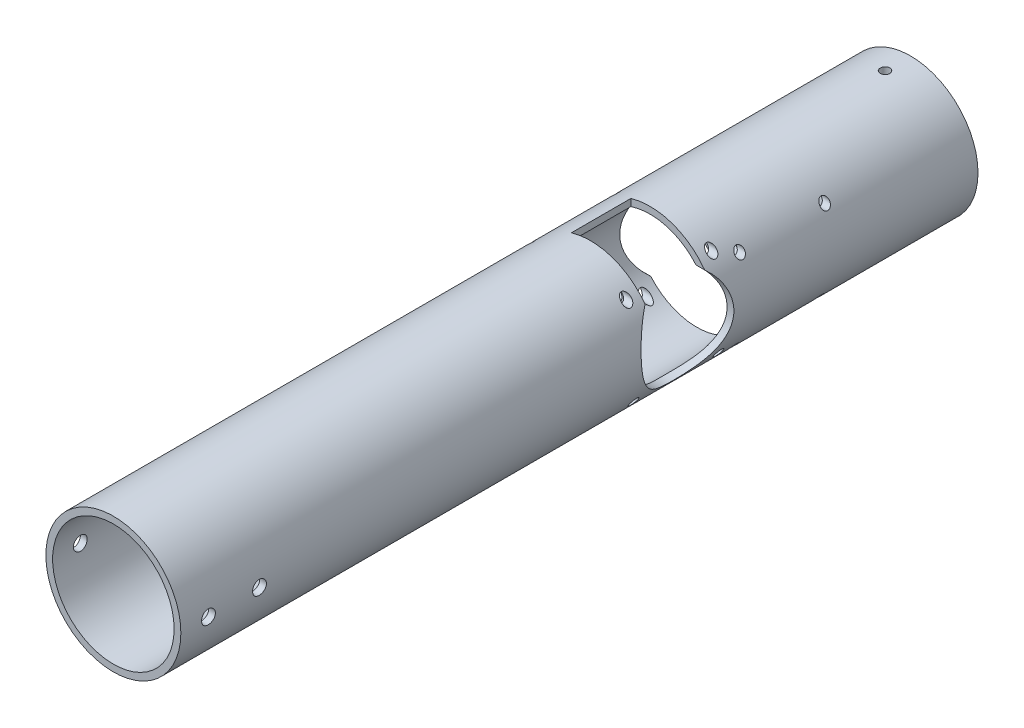
SolidWorks part; units mm, degrees
material "6061 Alloy"
ref_plane "Front Plane" through (0, 0, 0) normal (0, 0, 1) x (1, 0, 0)
ref_plane "Top Plane" through (0, 0, 0) normal (0, 1, 0) x (1, 0, 0)
ref_plane "Right Plane" through (0, 0, 0) normal (1, 0, 0) x (0, 0, -1)
sketch "Sketch1" plane through (0, 0, 0) normal (0, 0, 1) x (1, 0, 0)
  circle A0 centre (0, 0) radius 31.75
  circle A1 centre (0, 0) radius 28.575
  dimension "D1" = 63.5
  dimension "D2" = 57.15
extrude "Boss-Extrude1" add sketch "Sketch1" along normal blind 125 and the other way blind 250 contours A1 | A0
sketch "Sketch2" plane through (0, 0, 0) normal (1, 0, 0) x (0, 0, -1)
  circle A2 centre (163.488, -2) radius 21.75
  dimension "D1" = 43.5
  dimension "D2" = 163.488
  dimension "D3" = 2
extrude "Cut-Extrude1" cut sketch "Sketch2" against normal through all
sketch "Sketch3" plane through (0, 0, 0) normal (1, 0, 0) x (0, 0, -1)
  circle A1 centre (113.45, 2) radius 21.75
  dimension "D1" = 113.45
  dimension "D2" = 43.5
  dimension "D3" = 2
extrude "Cut-Extrude2" cut sketch "Sketch3" along normal through all
sketch "Sketch5" plane through (0, 0, 0) normal (1, 0, 0) x (0, 0, -1)
  line L1 (177.488, -12.75) -> (149.488, -12.75)
  line L2 (177.488, -12.75) -> (177.488, -34.75)
  line L3 (177.488, -34.75) -> (149.488, -34.75)
  line L4 (149.488, -12.75) -> (149.488, -34.75)
  line L5 (177.488, -12.75) -> (149.488, -34.75) construction
  line L6 (177.488, -34.75) -> (149.488, -12.75) construction
  circle A0 centre (163.488, -2) radius 21.75 construction
  circle A1 centre (163.488, -2) radius 21.75 construction
  point P0 (163.488, -23.75)
  dimension "D1" = 28
  dimension "D2" = 22
  dimension "D3" = 163.488
extrude "Cut-Extrude4" cut sketch "Sketch5" against normal through all from offset 9
sketch "Sketch6" plane through (0, 0, 0) normal (1, 0, 0) x (0, 0, -1)
  line L1 (99.45, 34.75) -> (127.45, 34.75)
  line L2 (99.45, 34.75) -> (99.45, 12.75)
  line L3 (99.45, 12.75) -> (127.45, 12.75)
  line L4 (127.45, 34.75) -> (127.45, 12.75)
  line L5 (99.45, 34.75) -> (127.45, 12.75) construction
  line L6 (99.45, 12.75) -> (127.45, 34.75) construction
  circle A0 centre (113.45, 2) radius 21.75 construction
  circle A1 centre (113.45, 2) radius 21.75 construction
  point P0 (113.45, 23.75)
  dimension "D1" = 28
  dimension "D2" = 22
  dimension "D3" = 113.45
extrude "Cut-Extrude5" cut sketch "Sketch6" along normal through all from offset 9 offset against normal yes
sketch "Sketch10" plane through (0, 0, 0) normal (1, 0, 0) x (0, 0, -1)
  line L1 (203.488, 38) -> (123.488, 38)
  line L2 (203.488, 38) -> (203.488, -42)
  line L3 (203.488, -42) -> (123.488, -42)
  line L4 (123.488, 38) -> (123.488, -42)
  line L5 (203.488, 38) -> (123.488, -42) construction
  line L6 (203.488, -42) -> (123.488, 38) construction
  point P0 (163.488, -2)
  dimension "D1" = 80
  dimension "D2" = 80
sketch "Sketch11" plane through (0, 0, 0) normal (1, 0, 0) x (0, 0, -1)
  line L0 (203.488, 38) -> (123.488, -42) construction
  line L1 (203.488, -42) -> (123.488, 38) construction
  circle A0 centre (183.488, 18) radius 2
  circle A1 centre (143.488, 18) radius 2
  circle A2 centre (143.488, -22) radius 2
  circle A3 centre (183.488, -22) radius 2
  dimension "D5" = 4
  dimension "D6" = 4
  dimension "D7" = 4
  dimension "D8" = 4
  dimension "D1" = 20
  dimension "D2" = 20
  dimension "D3" = 20
  dimension "D4" = 20
extrude "Cut-Extrude8" cut sketch "Sketch11" against normal through all both and the other way through all
sketch "Sketch12" plane through (0, 0, 0) normal (1, 0, 0) x (0, 0, -1)
  line L0 (-125, 31.75) -> (-125, -31.75) construction
  circle A0 centre (-112, 0) radius 3.25
  circle A1 centre (-88, 0) radius 3.25
  point P4 (-102.2745, 0)
  point P6 (0, 0)
  point P8 (0, 0)
  point P9 (0, 0)
  point P11 (0, 0)
  dimension "D1" = 6.5
  dimension "D2" = 6.5
  dimension "D3" = 24
  dimension "D4" = 13
extrude "Cut-Extrude10" cut sketch "Sketch12" against normal through all both and the other way through all
sketch "Sketch13" plane through (0, 0, 0) normal (0, 1, 0) x (1, 0, 0)
  line L0 (0, -34.925) -> (0, 34.925) construction
  line L1 (28.575, 250) -> (-28.575, 250) construction
  circle A0 centre (0, 238) radius 2.25
  dimension "D2" = 4.5
  dimension "D1" = 12
extrude "Cut-Extrude11" cut sketch "Sketch13" against normal through all both and the other way through all
sketch "Sketch14" plane through (0, 0, 0) normal (1, 0, 0) x (0, 0, -1)
  line L1 (88.45, 27) -> (138.45, 27)
  line L2 (88.45, 27) -> (88.45, -23)
  line L3 (88.45, -23) -> (138.45, -23)
  line L4 (138.45, 27) -> (138.45, -23)
  line L5 (88.45, 27) -> (138.45, -23) construction
  line L6 (88.45, -23) -> (138.45, 27) construction
  circle A0 centre (93.45, 22) radius 2
  circle A1 centre (133.45, 22) radius 2
  circle A2 centre (133.45, -18) radius 2
  circle A3 centre (93.45, -18) radius 2
  point P0 (113.45, 2)
  point P15 (0, 0)
  dimension "D4" = 4
  dimension "D5" = 4
  dimension "D6" = 4
  dimension "D7" = 4
  dimension "D1" = 50
  dimension "D2" = 50
  dimension "D3" = 20
  dimension "D8" = 20
  dimension "D9" = 20
  dimension "D10" = 20
sketch "Sketch15" plane through (0, 0, 0) normal (1, 0, 0) x (0, 0, -1)
  circle A0 centre (93.45, 22) radius 2
  circle A1 centre (133.45, 22) radius 2
  circle A2 centre (133.45, -18) radius 2
  circle A3 centre (93.45, -18) radius 2
extrude "Cut-Extrude12" cut sketch "Sketch15" against normal through all and the other way through all
hole_wizard "M4 Clearance Hole1" positions "Sketch18" profile "Sketch19" hole size "M4" standard "ANSI Metric"
sketch "Sketch18" plane through (0, 0, 0) normal (1, 0, 0) x (0, 0, -1)
  circle A0 centre (93.45, 22) radius 2 construction
  circle A1 centre (133.45, 22) radius 2 construction
  circle A2 centre (93.45, -18) radius 2 construction
  circle A3 centre (133.45, -18) radius 2 construction
  point P0 (93.45, 22)
  point P2 (133.45, 22)
  point P4 (93.45, -18)
  point P6 (133.45, -18)
  point P20 (183.488, 18)
  point P23 (143.488, 18)
  point P26 (183.488, -22)
  point P29 (143.488, -22)
sketch "Sketch19" plane through (0, 22, -93.45) normal (0, 1, 0) x (0, 0, 1)
  line L0 (0, 0) -> (0, 31.75)
  line L1 (0, 31.75) -> (2.25, 31.75)
  line L2 (2.25, 31.75) -> (2.25, 0)
  line L5 (2.25, 0) -> (0, 0)
  line L11 (0, -6.35) -> (0, 107.95) construction
  dimension "Thru Hole Dia." = 4.5
  dimension "Thru Hole Depth" = 31.75
mirror "Mirror1" about plane through (0, 0, 0) normal (1, 0, 0) of "M4 Clearance Hole1"
